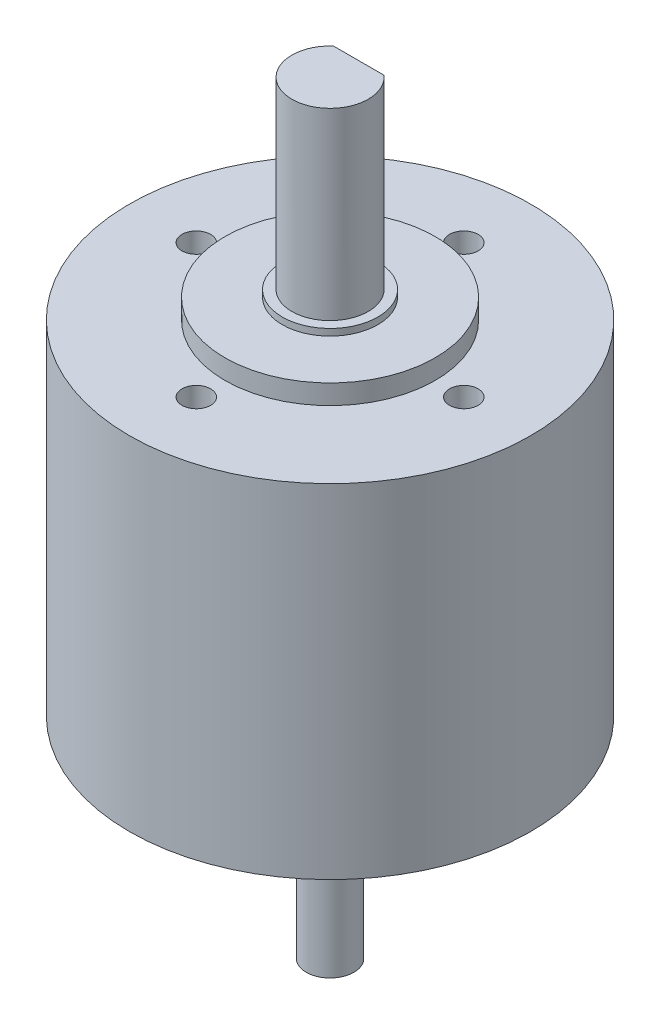
SolidWorks part; units mm, degrees
ref_plane "Front Plane" through (0, 0, 0) normal (0, 0, 1) x (1, 0, 0)
ref_plane "Top Plane" through (0, 0, 0) normal (0, 1, 0) x (1, 0, 0)
ref_plane "Right Plane" through (0, 0, 0) normal (1, 0, 0) x (0, 0, -1)
sketch "Sketch1" plane through (0, 0, 0) normal (0, 1, 0) x (1, 0, 0)
  circle A0 centre (0, 0) radius 21
  dimension "D1" = 42
extrude "Boss-Extrude1" add sketch "Sketch1" along normal mid plane 35.8902
sketch "Sketch2" plane through (0, 17.9451, 0) normal (0, 1, 0) x (1, 0, 0)
  circle A0 centre (0, 0) radius 11
  dimension "D1" = 22
extrude "Boss-Extrude2" add sketch "Sketch2" along normal mid plane 40.005 from surface at -17.9451 starting at plane "Top Plane"
sketch "Sketch3" plane through (0, 20.0025, 0) normal (0, 1, 0) x (1, 0, 0)
  circle A0 centre (0, 0) radius 4
  dimension "D1" = 8
extrude "Boss-Extrude4" add sketch "Sketch3" along normal offset from surface (19.9426 mm away) 22 up to face at (0, 17.9451, 11) offset beyond the face yes
sketch "Sketch4" plane through (0, 39.9451, 0) normal (0, 1, 0) x (1, 0, 0)
  line L0 (-2.6458, 3) -> (2.6458, 3)
  line L1 (0, -4) -> (0, 3) construction
  line L2 (0, 3) -> (0, 4) construction
  arc A0 (0, -4) -> (2.6458, 3) centre (0, 0) ccw construction
  circle A1 centre (0, 0) radius 4
  arc A2 (2.6458, 3) -> (-2.6458, 3) centre (0, 0) ccw
  arc A3 (-2.6458, 3) -> (0, -4) centre (0, 0) ccw construction
  dimension "D2" = 1
  dimension "D1" = 0
extrude "Cut-Extrude1" cut sketch "Sketch4" against normal blind 15
sketch "Sketch5" plane through (0, 17.9451, 0) normal (0, 1, 0) x (1, 0, 0)
  circle A0 centre (0, 0) radius 14 construction
  circle A1 centre (0, 14) radius 1.5
  circle A2 centre (-14, 0) radius 1.5
  circle A3 centre (0, -14) radius 1.5
  circle A4 centre (14, 0) radius 1.5
  dimension "D1" = 28
  dimension "D2" = 3
extrude "Cut-Extrude2" cut sketch "Sketch5" against normal blind 4
sketch "Sketch6" plane through (0, -20.0025, 0) normal (0, -1, 0) x (1, 0, 0)
  circle A0 centre (0, 0) radius 2.5
  dimension "D1" = 5
extrude "Boss-Extrude5" add sketch "Sketch6" along normal offset from surface (19.9426 mm away) 22 up to face at (0, -17.9451, 11) offset beyond the face yes
sketch "Sketch7" plane through (0, -39.9451, 0) normal (0, -1, 0) x (1, 0, 0)
  line L0 (-2, -1.5) -> (2, -1.5)
  line L1 (0, -1.5) -> (0, -2.5) construction
  arc A0 (2, -1.5) -> (-2, -1.5) centre (0, 0) cw
  circle A2 centre (0, 0) radius 2.5 construction
  dimension "D1" = 1
extrude "Cut-Extrude3" cut sketch "Sketch7" against normal offset from surface (16.9426 mm away) 3 up to face at (0, -20.0025, -2.5)
sketch "Sketch9" plane through (0, 0, 0) normal (0, 1, 0) x (1, 0, 0)
  circle A0 centre (0, 0) radius 5
  dimension "D1" = 10
extrude "Boss-Extrude6" add sketch "Sketch9" along normal mid plane 41.402
